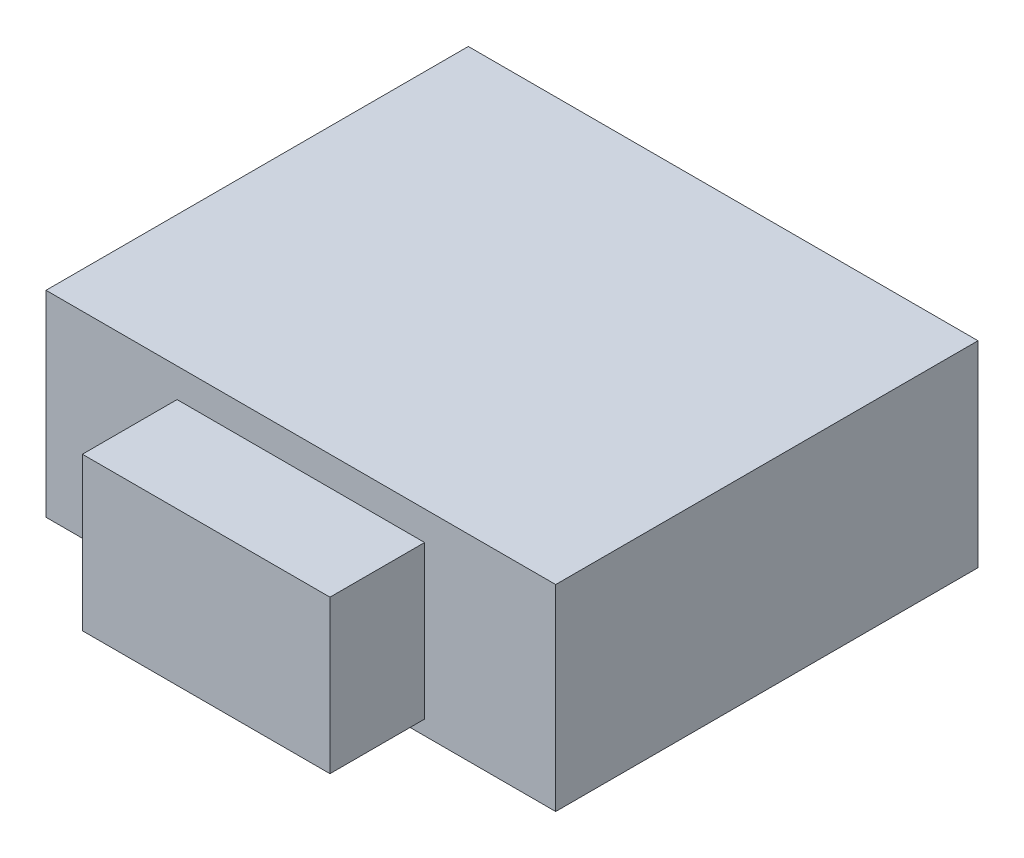
SolidWorks part; units mm, degrees
ref_plane "Front Plane" through (0, 0, 0) normal (0, 0, 1) x (1, 0, 0)
ref_plane "Top Plane" through (0, 0, 0) normal (0, 1, 0) x (1, 0, 0)
ref_plane "Right Plane" through (0, 0, 0) normal (1, 0, 0) x (0, 0, -1)
sketch "Sketch1" plane through (0, 0, 0) normal (0, 0, -1) x (1, 0, 0)
  line L1 (-1.75, 0) -> (1.75, 0)
  line L2 (-1.75, 0) -> (-1.75, 1.35)
  line L3 (-1.75, 1.35) -> (1.75, 1.35)
  line L4 (1.75, 0) -> (1.75, 1.35)
  point P4 (0, 0)
  dimension "D1" = 3.5
  dimension "D2" = 1.35
extrude "Boss-Extrude1" add sketch "Sketch1" along normal blind 2.9
sketch "Sketch2" plane through (0, 0, 0) normal (0, 0, 1) x (1, 0, 0)
  line L0 (-1.75, 0) -> (1.75, 0) construction
  line L1 (0.85, -1.25) -> (-0.85, -1.25)
  line L2 (0.85, -1.25) -> (0.85, -0.2)
  line L3 (0.85, -0.2) -> (-0.85, -0.2)
  line L4 (-0.85, -1.25) -> (-0.85, -0.2)
  line L5 (0.85, -1.25) -> (-0.85, -0.2) construction
  line L6 (0.85, -0.2) -> (-0.85, -1.25) construction
  line L7 (1.75, -1.35) -> (-1.75, -1.35) construction
  point P0 (0, -0.725)
  dimension "D1" = 1.7
  dimension "D2" = 0.2
  dimension "D3" = 0.1
extrude "Boss-Extrude2" add sketch "Sketch2" along normal blind 0.65
